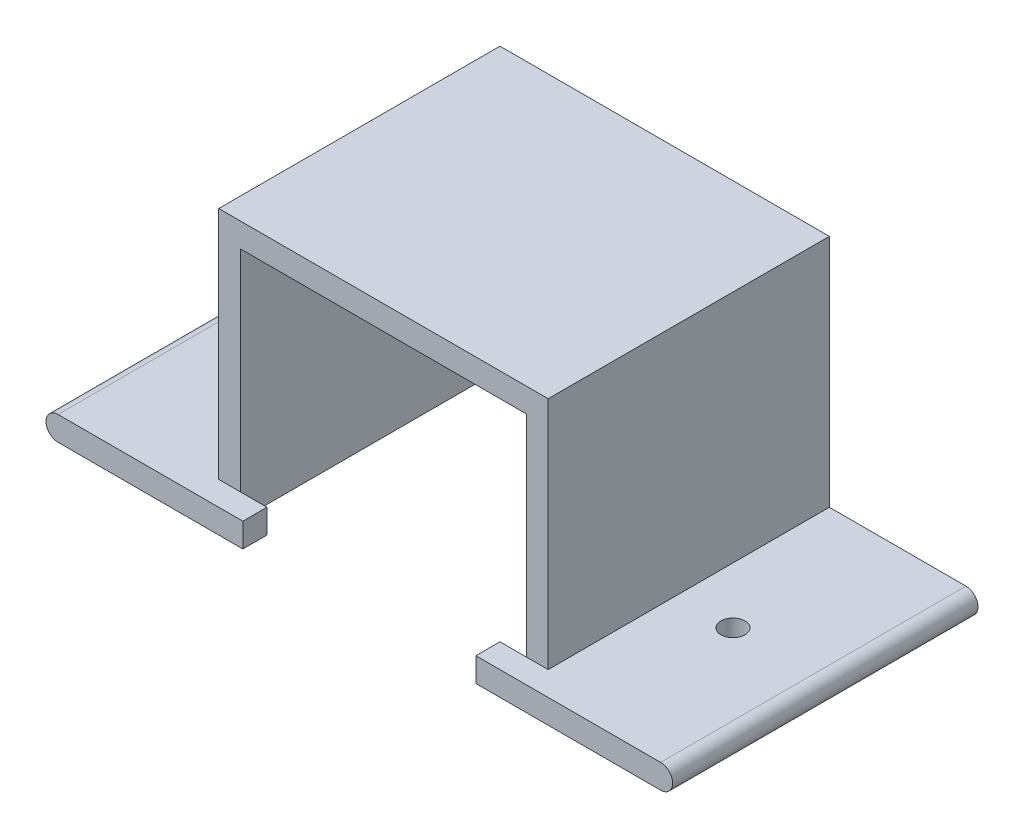
SolidWorks part; units mm, degrees
ref_plane "Front Plane" through (0, 0, 0) normal (0, 0, 1) x (1, 0, 0)
ref_plane "Top Plane" through (0, 0, 0) normal (0, 1, 0) x (1, 0, 0)
ref_plane "Right Plane" through (0, 0, 0) normal (1, 0, 0) x (0, 0, -1)
sketch "Sketch1" plane through (0, 0, 0) normal (0, 0, 1) x (1, 0, 0)
  line L0 (0, 0) -> (-19.7, 0)
  line L4 (-55.3, 0) -> (-75, 0)
  line L5 (0, 3) -> (-17, 3)
  line L6 (-17, 3) -> (-17, 30.2)
  line L8 (-58, 30.2) -> (-58, 3)
  line L9 (-58, 3) -> (-75, 3)
  line L11 (-20, 29.2) -> (-55, 29.2)
  line L13 (-17, 30.2) -> (-17, 32.2)
  line L14 (-20, 27.2) -> (-55, 27.2) construction
  line L15 (-17, 32.2) -> (-58, 32.2)
  line L16 (-58, 32.2) -> (-58, 30.2)
  line L17 (-17, 30.2) -> (-58, 30.2) construction
  line L18 (-55, 29.2) -> (-55.3, 29.2)
  line L19 (-55.3, 29.2) -> (-55.3, 0)
  line L20 (-55, 0) -> (-75, 0) construction
  line L21 (-55, 27.2) -> (-55, 0) construction
  line L22 (-20, 29.2) -> (-19.7, 29.2)
  line L23 (-19.7, 29.2) -> (-19.7, 0)
  line L24 (0, 0) -> (-20, 0) construction
  line L25 (-20, 0) -> (-20, 27.2) construction
  arc A0 (0, 0) -> (0, 3) centre (0, 1.5) ccw
  arc A1 (-75, 0) -> (-75, 3) centre (-75, 1.5) cw
  dimension "D1" = 3
extrude "Boss-Extrude1" add sketch "Sketch1" along normal blind 32
sketch "Sketch2" plane through (0, 0, 0) normal (0, 0, -1) x (-1, 0, 0)
  line L0 (75, 0) -> (55.3, 0)
  line L1 (75, 0) -> (55.3, 0)
  line L2 (55.3, 0) -> (55.3, 29.2)
  line L4 (19.7, 29.2) -> (19.7, 0)
  line L8 (19.7, 0) -> (0, 0)
  line L9 (19.7, 0) -> (0, 0)
  line L10 (0, 3) -> (17, 3)
  line L11 (0, 3) -> (17, 3)
  line L12 (17, 3) -> (17, 32.2)
  line L13 (17, 3) -> (17, 32.2)
  line L14 (17, 32.2) -> (58, 32.2)
  line L16 (58, 32.2) -> (58, 3)
  line L17 (58, 32.2) -> (58, 3)
  line L18 (58, 3) -> (75, 3)
  line L19 (58, 3) -> (75, 3)
  line L20 (55.3, 0) -> (19.7, 0)
  line L21 (55.3, 0) -> (55.3, 29.2)
  line L23 (55.3, 29.2) -> (19.7, 29.2)
  line L24 (19.7, 29.2) -> (19.7, 0)
  line L28 (17, 32.2) -> (58, 32.2)
  arc A0 (0, 3) -> (0, 0) centre (0, 1.5) ccw
  arc A1 (0, 3) -> (0, 0) centre (0, 1.5) ccw
  arc A2 (75, 0) -> (75, 3) centre (75, 1.5) ccw
  arc A3 (75, 0) -> (75, 3) centre (75, 1.5) ccw
  arc M2 (0, 3) -> (0, 0) centre (0, 1.5) ccw
  line M3 (0, 0) -> (19.7, 0)
  line M7 (55.3, 0) -> (75, 0)
  arc M8 (75, 0) -> (75, 3) centre (75, 1.5) ccw
  line M9 (75, 3) -> (58, 3)
  line M10 (58, 3) -> (58, 32.2)
  line M12 (17, 32.2) -> (17, 3)
  line M13 (17, 3) -> (0, 3)
  line M24 (19.7, 29.2) -> (55.3, 29.2)
  line M25 (58, 32.2) -> (17, 32.2)
  line M26 (19.7, 0) -> (19.7, 29.2)
  line M27 (55.3, 29.2) -> (55.3, 0)
extrude "Boss-Extrude2" add sketch "Sketch2" along normal blind 3 contours L20 M27 M24 M26 | M13 M2 M3 M26 M24 M27 M7 M8 M9 M10 M25 M12
sketch "Sketch3" plane through (0, 0, 32) normal (0, 0, 1) x (1, 0, 0)
  line L4 (-20, 0) -> (-23, 0)
  line L5 (-23, 0) -> (-23, 3)
  line L6 (-23, 3) -> (-20, 3)
  line L9 (-20, 3) -> (0, 3)
  line L10 (0, 3) -> (-17, 3) construction
  line L11 (-20, 0) -> (0, 0)
  line L12 (-20, 8.4579) -> (-55, 8.4579) construction
  line L14 (-37.5, 8.4579) -> (-37.5, -0.8521) construction
  line L15 (-55, 0) -> (-75, 0)
  line L16 (-55, 3) -> (-75, 3)
  line L17 (-52, 3) -> (-55, 3)
  line L18 (-52, 0) -> (-52, 3)
  line L19 (-55, 0) -> (-52, 0)
  arc A0 (0, 0) -> (0, 3) centre (0, 1.5) ccw
  arc A1 (-75, 0) -> (-75, 3) centre (-75, 1.5) cw
  point P2 (0, 0)
  point P8 (0, 0)
extrude "Boss-Extrude3" add sketch "Sketch3" along normal blind 3
sketch "Sketch4" plane through (0, 0, 0) normal (0, -1, 0) x (1, 0, 0)
  line L0 (-55, 16) -> (-75, 16) construction
  line L2 (-75, 35) -> (-75, -3) construction
  line L3 (-55, 16) -> (-20, 16) construction
  line L5 (-20, 16) -> (-37.5, 16) construction
  line L6 (-37.5, 16) -> (-37.5, 23.8364) construction
  circle A0 centre (-65, 16) radius 1.5
  circle A1 centre (-10, 16) radius 1.5
  point P10 (0, 0)
  point P15 (0, 0)
extrude "Cut-Extrude1" cut sketch "Sketch4" against normal blind 4
